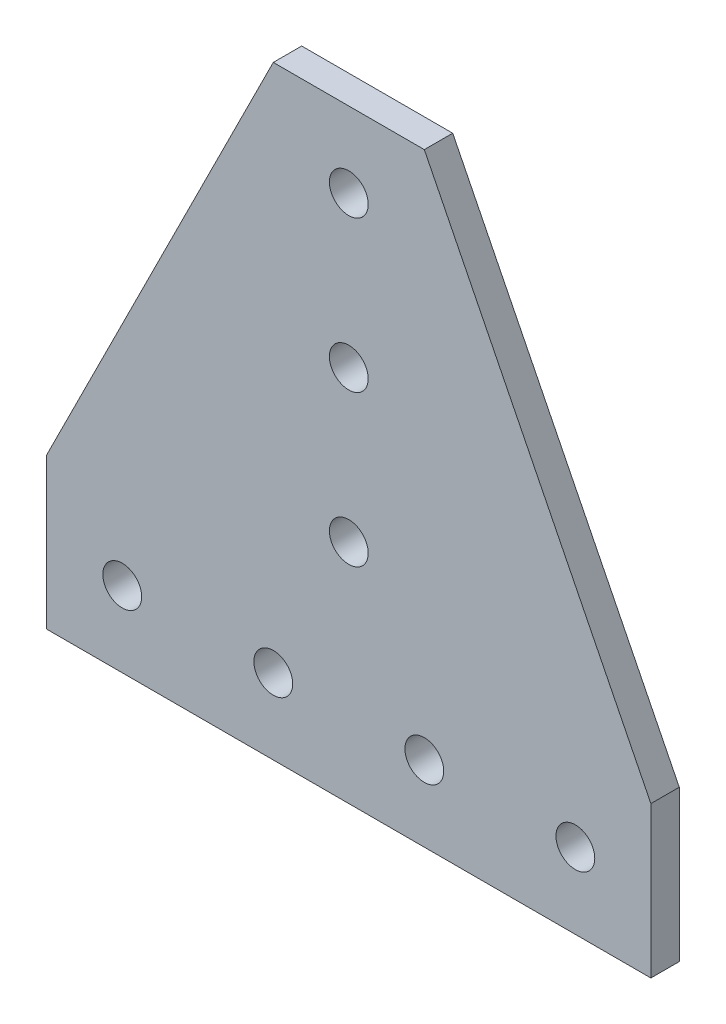
SolidWorks part; units mm, degrees
ref_plane "Front Plane" through (0, 0, 0) normal (0, 0, 1) x (1, 0, 0)
ref_plane "Top Plane" through (0, 0, 0) normal (0, 1, 0) x (1, 0, 0)
ref_plane "Right Plane" through (0, 0, 0) normal (1, 0, 0) x (0, 0, -1)
sketch "Sketch1" plane through (0, 0, 0) normal (0, 0, 1) x (1, 0, 0)
  line L0 (50.8, -50.8) -> (-50.8, -50.8) construction
  line L1 (0, 50.8) -> (0, -50.8) construction
  line L2 (50.8, -50.8) -> (50.8, -25.4) construction
  line L3 (-41.3639, -38.1) -> (-34.8361, -38.1) construction
  point P0 (50.8, -38.1)
  point P3 (0, -50.8)
  point P7 (0, 0)
  point P9 (-12.7, -38.1)
  point P12 (-38.1, -38.1)
  point P18 (50.8, 50.8)
sketch "Sketch2" plane through (0, 0, 0) normal (1, 0, 0) x (0, 0, -1)
  line L0 (2.3876, 0) -> (-2.3876, 0) construction
  point P4 (0, 0)
  dimension "Thickness" = 4.7752
sketch "Sketch3" plane through (0, 0, 0) normal (0, 0, 1) x (1, 0, 0)
  line L0 (50.8, -50.8) -> (-50.8, -50.8)
  line L1 (50.8, -50.8) -> (50.8, -25.4)
  line L2 (50.8, -25.4) -> (12.7, 50.8)
  line L3 (12.7, 50.8) -> (-12.7, 50.8)
  line L4 (50.8, -50.8) -> (-50.8, -50.8) construction
  line L5 (0, -50.8) -> (0, 50.8) construction
  line L6 (-50.8, -25.4) -> (-12.7, 50.8)
  line L7 (-50.8, -50.8) -> (-50.8, -25.4)
extrude "Boss-Extrude1" add sketch "Sketch3" against normal up to vertex (2.3876 mm away) and the other way up to vertex (2.3876 mm away) contours L3 L6 L7 L0 L1 L2 up to point (0, 0, -2.3876) other way up to point (0, 0, 2.3876)
sketch "Sketch4" plane through (0, 0, 2.3876) normal (0, 0, 1) x (1, 0, 0)
  line L0 (0, -50.8) -> (0, 50.8) construction
  line L1 (50.8, -50.8) -> (-50.8, -50.8) construction
  line L2 (12.7, 50.8) -> (-12.7, 50.8) construction
  line L3 (-41.3639, -38.1) -> (-34.8361, -38.1) construction
  line L4 (-38.1, -38.1) -> (-12.7, -38.1) construction
  line L5 (0, 38.1) -> (0, 12.7) construction
  circle A0 centre (-38.1, -38.1) radius 3.2639
  circle A5 centre (-12.7, -38.1) radius 3.2639
  circle A6 centre (12.7, -38.1) radius 3.2639
  circle A9 centre (0, 38.1) radius 3.2639
  circle A10 centre (0, 12.7) radius 3.2639
  circle A11 centre (38.1, -38.1) radius 3.2639
  circle A12 centre (0, -12.7) radius 3.2639
  dimension "D2" = 25.4
  dimension "D3" = 12.7
  dimension "D5" = 25.4
  dimension "D1" = 4
  dimension "D4" = 3
extrude "Cut-Extrude1" cut sketch "Sketch4" against normal through all
equation "\"D1@Sketch4\"=\"#Holes@Sketch1\""
equation "\"D2@Sketch4\"=\"Hole Spacing@Sketch1\""
equation "\"D3@Sketch4\"=\"Hole to Edge@Sketch1\""
equation "\"D5@Sketch4\"=\"Hole Spacing@Sketch1\""
equation "\"D4@Sketch4\"=\"#Holes@Sketch1\"-1"
